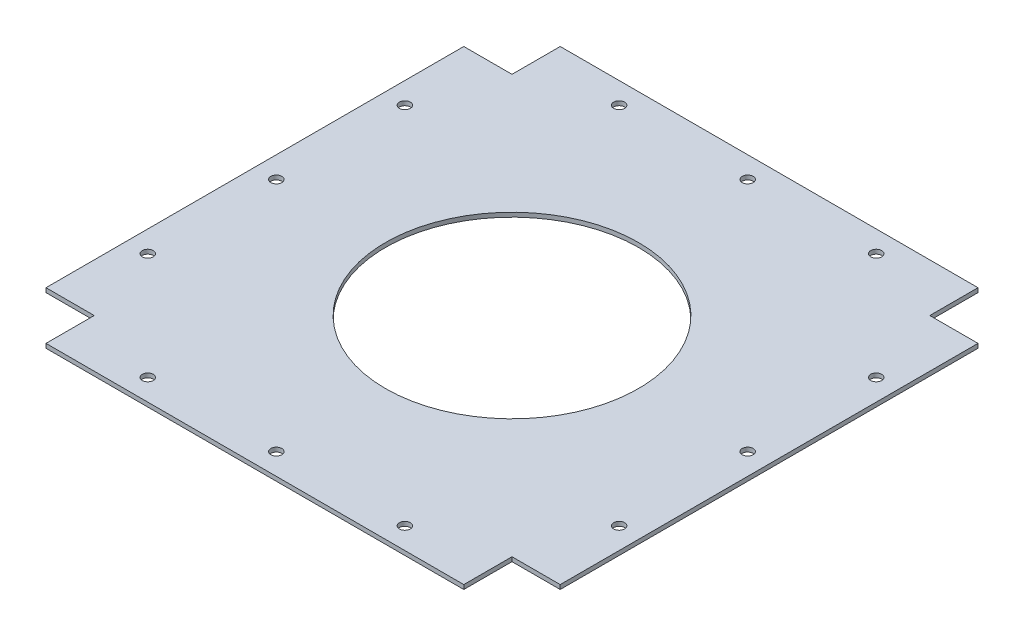
SolidWorks part; units mm, degrees
ref_plane "Front Plane" through (0, 0, 0) normal (0, 0, 1) x (1, 0, 0)
ref_plane "Top Plane" through (0, 0, 0) normal (0, 1, 0) x (1, 0, 0)
ref_plane "Right Plane" through (0, 0, 0) normal (1, 0, 0) x (0, 0, -1)
sketch "Sketch1" plane through (0, 0, 0) normal (0, 1, 0) x (1, 0, 0)
  line L0 (123.825, 152.4) -> (123.825, 123.825)
  line L1 (-123.825, -152.4) -> (123.825, -152.4)
  line L2 (-152.4, -123.825) -> (-152.4, 123.825)
  line L3 (-123.825, 152.4) -> (123.825, 152.4)
  line L4 (152.4, -123.825) -> (152.4, 123.825)
  line L5 (-152.4, -152.4) -> (152.4, 152.4) construction
  line L6 (-152.4, 152.4) -> (152.4, -152.4) construction
  line L7 (123.825, 123.825) -> (152.4, 123.825)
  line L8 (-152.4, -123.825) -> (-123.825, -123.825)
  line L9 (-123.825, -123.825) -> (-123.825, -152.4)
  line L10 (152.4, 0) -> (-152.4, 0) construction
  line L11 (123.825, -123.825) -> (152.4, -123.825)
  line L12 (123.825, -152.4) -> (123.825, -123.825)
  line L13 (-152.4, 123.825) -> (-123.825, 123.825)
  line L14 (-123.825, 123.825) -> (-123.825, 152.4)
  line L15 (123.825, 139.7) -> (-123.825, 139.7) construction
  circle A0 centre (76.2, 139.7) radius 3.2385
  circle A1 centre (0, 139.7) radius 3.2385
  circle A2 centre (-76.2, 139.7) radius 3.2385
  circle A3 centre (-76.2, -139.7) radius 3.2385
  circle A4 centre (0, -139.7) radius 3.2385
  circle A5 centre (76.2, -139.7) radius 3.2385
  circle A6 centre (139.7, -76.2) radius 3.2385
  circle A7 centre (139.7, 0) radius 3.2385
  circle A8 centre (139.7, 76.2) radius 3.2385
  circle A9 centre (-139.7, 76.2) radius 3.2385
  circle A10 centre (-139.7, 0) radius 3.2385
  circle A11 centre (-139.7, -76.2) radius 3.2385
  circle A12 centre (0, 0) radius 75
  point P0 (0, 0)
  dimension "D4" = 6.477
  dimension "D7" = 150
  dimension "D1" = 304.8
  dimension "D2" = 28.575
  dimension "D3" = 12.7
  dimension "D5" = 76.2
  dimension "D6" = 76.2
extrude "Boss-Extrude1" add sketch "Sketch1" along normal blind 2.54
